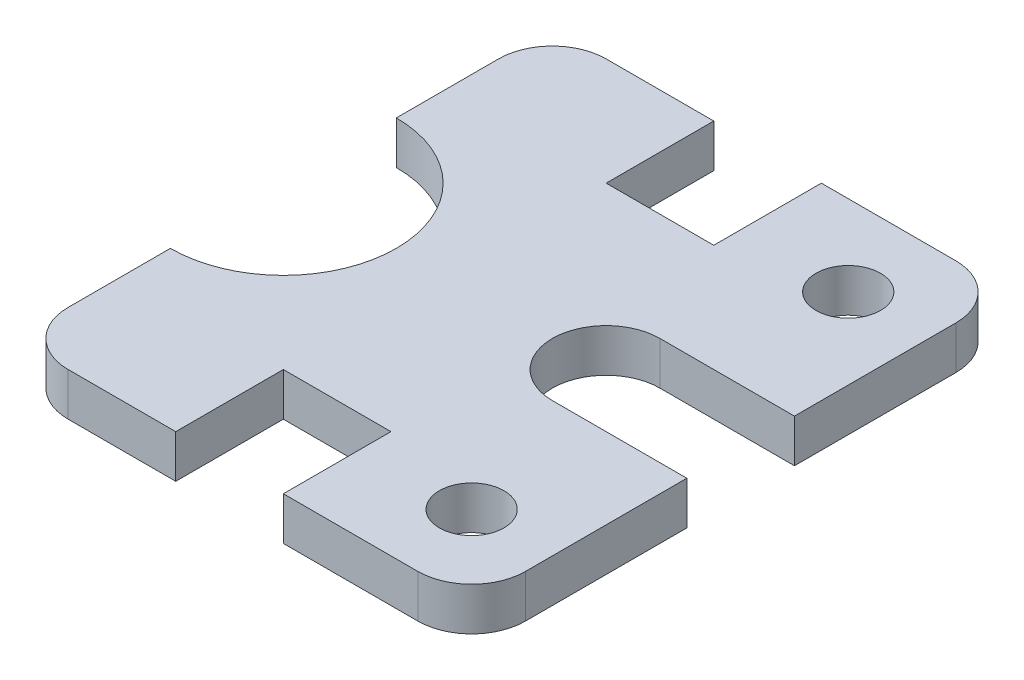
SolidWorks part; units mm, degrees
ref_plane "Front Plane" through (0, 0, 0) normal (0, 0, 1) x (1, 0, 0)
ref_plane "Top Plane" through (0, 0, 0) normal (0, 1, 0) x (1, 0, 0)
ref_plane "Right Plane" through (0, 0, 0) normal (1, 0, 0) x (0, 0, -1)
sketch "Sketch1" plane through (0, 0, 0) normal (0, 1, 0) x (1, 0, 0)
  line L5 (-25.1017, -0.1157) -> (-0.1017, -0.1157)
  line L6 (-85.1017, 10.8843) -> (-85.1017, 29.8843)
  line L8 (-0.1017, 29.8843) -> (-0.1017, -0.1157)
  line L9 (-75.1017, 39.8843) -> (-55.1017, 39.8843)
  line L11 (-55.1017, 39.8843) -> (-55.1017, 19.8843)
  line L12 (-55.1017, 19.8843) -> (-35.1017, 19.8843)
  line L13 (-35.1017, 39.8843) -> (-35.1017, 19.8843)
  line L14 (-35.1017, 39.8843) -> (-10.1017, 39.8843)
  line L15 (-35.1017, -60.1157) -> (-10.1017, -60.1157)
  line L16 (-35.1017, -60.1157) -> (-35.1017, -40.1157)
  line L17 (-55.1017, -40.1157) -> (-35.1017, -40.1157)
  line L18 (-55.1017, -60.1157) -> (-55.1017, -40.1157)
  line L19 (-75.1017, -60.1157) -> (-55.1017, -60.1157)
  line L20 (-0.1017, -50.1157) -> (-0.1017, -20.1157)
  line L21 (-85.1017, -31.1157) -> (-85.1017, -50.1157)
  line L22 (-25.1017, -20.1157) -> (-0.1017, -20.1157)
  circle A1 centre (-15.1017, 24.8843) radius 6
  arc A2 (-25.1017, -20.1157) -> (-25.1017, -0.1157) centre (-25.1017, -10.1157) cw
  arc A3 (-85.1017, 29.8843) -> (-75.1017, 39.8843) centre (-75.1017, 29.8843) cw
  arc A4 (-10.1017, 39.8843) -> (-0.1017, 29.8843) centre (-10.1017, 29.8843) cw
  circle A7 centre (-15.1017, -45.1157) radius 6
  arc A9 (-0.1017, -50.1157) -> (-10.1017, -60.1157) centre (-10.1017, -50.1157) cw
  arc A10 (-85.1017, -31.1157) -> (-85.1017, 10.8843) centre (-85.1017, -10.1157) ccw
  arc A11 (-85.1017, -50.1157) -> (-75.1017, -60.1157) centre (-75.1017, -50.1157) ccw
  point P1 (-85.1017, -60.1157)
  point P6 (-85.1017, -50.1157)
  point P9 (-85.1017, -50.1157)
  point P20 (-85.1017, -50.1157)
  point P23 (-85.1017, -60.1157)
  point P29 (-85.1017, -60.3723)
  point P38 (-85.1017, -60.1157)
  point P50 (-0.1017, -60.1157)
  dimension "D4" = 12
  dimension "D7" = 10
  dimension "D1" = 10
  dimension "D2" = 10
  dimension "D8" = 15
  dimension "D14" = 15
  dimension "D15" = 29
  dimension "D23" = 60
  dimension "D28" = 15
  dimension "D17" = 10
  dimension "D12" = 21
  dimension "D22" = 10
  dimension "D19" = 12
  dimension "D5" = 85
  dimension "D6" = 20
  dimension "D9" = 35
  dimension "D10" = 25
  dimension "D11" = 20
  dimension "D13" = 29
  dimension "D16" = 40
  dimension "D18" = 20
  dimension "D20" = 20
  dimension "D21" = 30
  dimension "D24" = 35
  dimension "D25" = 50
  dimension "D26" = 100
  dimension "D27" = 20
  dimension "D31" = 42
  dimension "D32" = 20
  dimension "D34" = 25
  dimension "D37" = 0.1017
  dimension "D38" = 0.1157
extrude "Boss-Extrude1" add sketch "Sketch1" along normal blind 8
